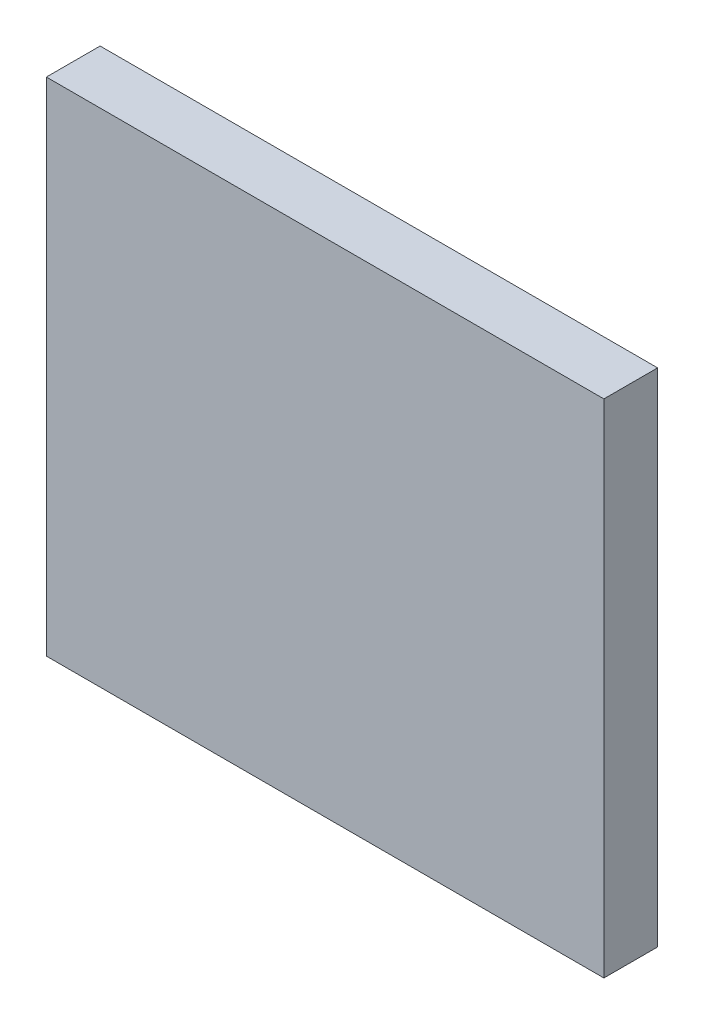
SolidWorks part; units mm, degrees
ref_plane "Plan de face" through (0, 0, 0) normal (0, 0, 1) x (1, 0, 0)
ref_plane "Plan de dessus" through (0, 0, 0) normal (0, 1, 0) x (1, 0, 0)
ref_plane "Plan de droite" through (0, 0, 0) normal (1, 0, 0) x (0, 0, -1)
sketch "Esquisse1" plane through (0, 0, 0) normal (0, 0, 1) x (1, 0, 0)
  line L1 (0, 0) -> (-124.5, 0)
  line L2 (0, 0) -> (0, 112)
  line L3 (0, 112) -> (-124.5, 112)
  line L4 (-124.5, 0) -> (-124.5, 112)
  dimension "D1" = 124.5
  dimension "D2" = 112
extrude "Boss.-Extru.1" add sketch "Esquisse1" along normal blind 12
